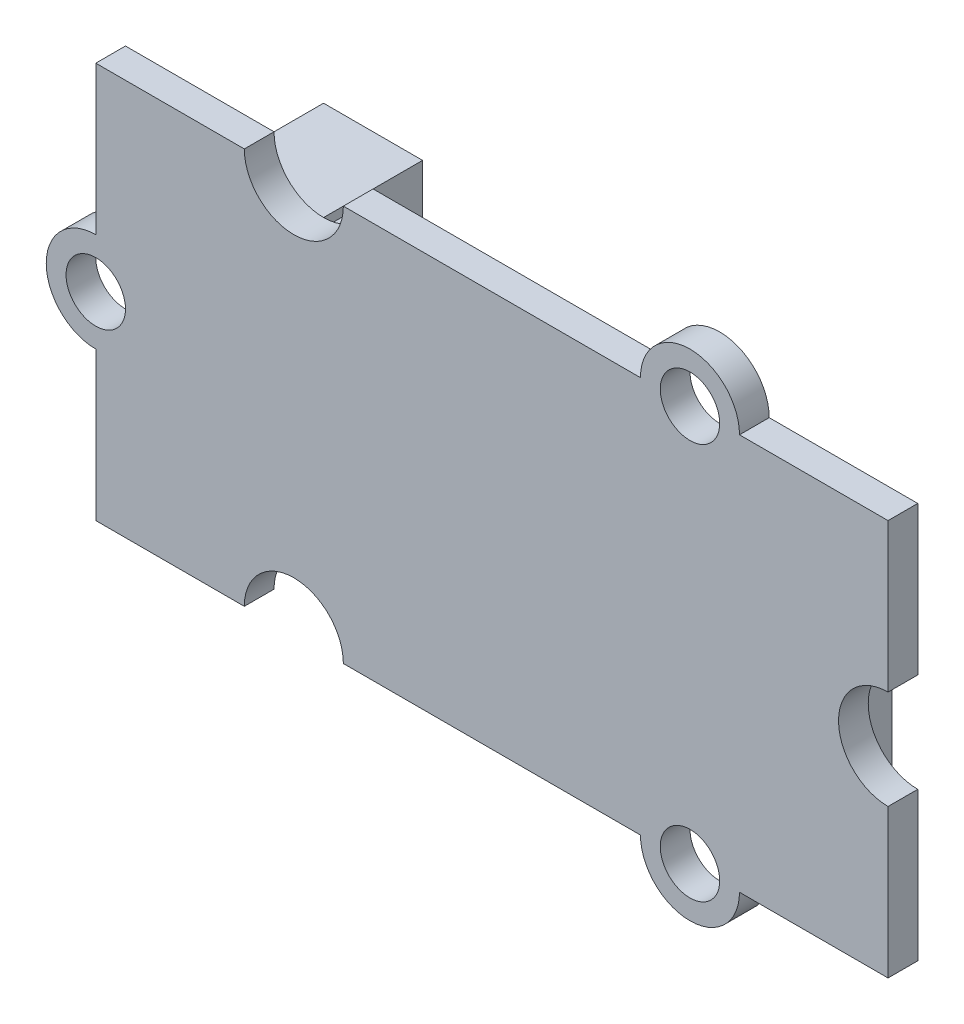
SolidWorks part; units mm, degrees
ref_plane "Ebene vorne" through (0, 0, 0) normal (0, 0, 1) x (1, 0, 0)
ref_plane "Ebene oben" through (0, 0, 0) normal (0, 1, 0) x (1, 0, 0)
ref_plane "Ebene rechts" through (0, 0, 0) normal (1, 0, 0) x (0, 0, -1)
sketch "Skizze1" plane through (0, 0, 0) normal (0, 0, 1) x (1, 0, 0)
  line L1 (-20, -10) -> (20, -10)
  line L2 (-20, -10) -> (-20, 10)
  line L3 (-20, 10) -> (20, 10)
  line L4 (20, -10) -> (20, 10)
  line L5 (-20, -10) -> (20, 10) construction
  line L6 (-20, 10) -> (20, -10) construction
  point P0 (0, 0)
  dimension "D1" = 40
  dimension "D2" = 20
extrude "Aufsatz-Linear austragen1" add sketch "Skizze1" along normal blind 1.5
sketch "Skizze2" plane through (0, 0, 1.5) normal (0, 0, 1) x (1, 0, 0)
  line L0 (20, -10) -> (20, 10) construction
  circle A0 centre (20, 0) radius 2.5
  point P2 (20, 0)
  dimension "D2" = 5
  dimension "D1" = 0
extrude "Schnitt-Linear austragen1" cut sketch "Skizze2" against normal through all
sketch "Skizze3" plane through (0, 0, 1.5) normal (0, 0, 1) x (1, 0, 0)
  line L0 (20, 10) -> (-20, 10) construction
  circle A0 centre (-10, 10) radius 2.5
  circle A1 centre (-10, -10) radius 2.5
  dimension "D1" = 5
  dimension "D2" = 10
  dimension "D3" = 2
extrude "Schnitt-Linear austragen2" cut sketch "Skizze3" against normal through all
sketch "Skizze4" plane through (0, 0, 1.5) normal (0, 0, 1) x (1, 0, 0)
  line L0 (20, 10) -> (-7.5, 10) construction
  line L1 (20, 2.5) -> (20, 10) construction
  circle A0 centre (10, 10) radius 2.5
  circle A1 centre (10, -10) radius 2.5
  dimension "D1" = 5
  dimension "D2" = 10
  dimension "D3" = 2
extrude "Aufsatz-Linear austragen2" add sketch "Skizze4" against normal up to surface (1.5 mm away) up to face at (-0.25, 0, 0)
sketch "Skizze5" plane through (0, 0, 0) normal (0, 0, -1) x (-1, 0, 0)
  line L0 (20, 10) -> (20, -10) construction
  circle A0 centre (20, 0) radius 2.5
  dimension "D1" = 5
extrude "Aufsatz-Linear austragen3" add sketch "Skizze5" against normal up to surface (1.5 mm away) up to face at (2.6786, 0, 1.5)
sketch "Skizze6" plane through (0, 0, 1.5) normal (0, 0, 1) x (1, 0, 0)
  line L0 (-7.5, -10) -> (7.5, -10) construction
  circle A0 centre (-20, 0) radius 1.5
  circle A1 centre (10, 10) radius 1.5
  circle A2 centre (10, -10) radius 1.5
  dimension "D1" = 3
  dimension "D2" = 3
  dimension "D4" = 3
  dimension "D3" = 0
extrude "Schnitt-Linear austragen3" cut sketch "Skizze6" against normal through all
sketch "Skizze7" plane through (0, 0, 0) normal (0, 0, -1) x (-1, 0, 0)
  line L0 (-20, -10) -> (-20, -2.5) construction
  line L1 (-17.2, 6.75) -> (10.3, 6.75)
  line L2 (-17.2, 6.75) -> (-17.2, -6.75)
  line L3 (-17.2, -6.75) -> (10.3, -6.75)
  line L4 (10.3, 6.75) -> (10.3, -6.75)
  line L5 (-17.2, 6.75) -> (10.3, -6.75) construction
  line L6 (-17.2, -6.75) -> (10.3, 6.75) construction
  point P0 (-3.45, 0)
  dimension "D1" = 27.5
  dimension "D2" = 13.5
  dimension "D3" = 0
  dimension "D4" = 2.8
extrude "Aufsatz-Linear austragen4" add sketch "Skizze7" along normal blind 1.5 separate body
sketch "Skizze8" plane through (0, 0, 0) normal (0, 0, -1) x (-1, 0, 0)
  line L0 (20, 10) -> (20, 2.5) construction
  line L1 (17.5, -5) -> (12.5, -5)
  line L2 (17.5, -5) -> (17.5, 5)
  line L3 (17.5, 5) -> (12.5, 5)
  line L4 (12.5, -5) -> (12.5, 5)
  line L5 (17.5, -5) -> (12.5, 5) construction
  line L6 (17.5, 5) -> (12.5, -5) construction
  point P0 (15, 0)
  dimension "D1" = 10
  dimension "D2" = 5
  dimension "D3" = 0
  dimension "D4" = 2.5
extrude "Aufsatz-Linear austragen5" add sketch "Skizze8" along normal blind 7.5 separate body
shell "Wandung1" thickness 0.5
sketch "Skizze10" plane through (0, 0, -0.5) normal (0, 0, -1) x (-1, 0, 0)
  line L0 (12.5, 5) -> (12.5, -5) construction
  line L1 (12.5, -5) -> (17.5, -5) construction
  circle A0 centre (15, -2.75) radius 0.75
  circle A1 centre (15, -0.75) radius 0.75
  circle A2 centre (15, 1.25) radius 0.75
  circle A3 centre (15, 3.25) radius 0.75
  dimension "D2" = 1.5
  dimension "D1" = 2.5
  dimension "D4" = 2.25
  dimension "D3" = 4
extrude "Aufsatz-Linear austragen6" add sketch "Skizze10" along normal blind 6.5
fillet "Verrundung1" radius 0.5 4 edges at (-15.75, 3.25, -7) (-15.75, 1.25, -7) (-15.75, -0.75, -7) (-15.75, -2.75, -7)
